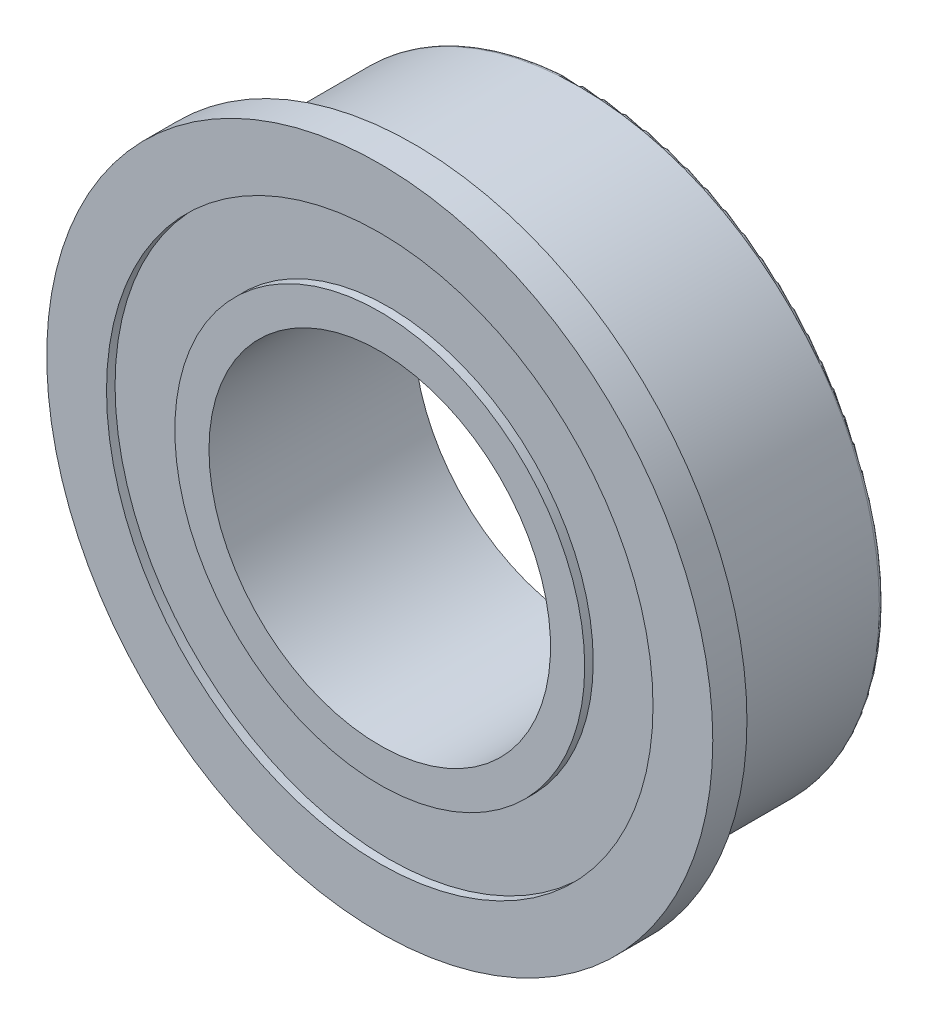
SolidWorks part; units mm, degrees
ref_plane "前基準面" through (0, 0, 0) normal (0, 0, 1) x (1, 0, 0)
ref_plane "上基準面" through (0, 0, 0) normal (0, 1, 0) x (1, 0, 0)
ref_plane "右基準面" through (0, 0, 0) normal (1, 0, 0) x (0, 0, -1)
sketch "草圖1" plane through (0, 0, 0) normal (0, 0, 1) x (1, 0, 0)
  circle A0 centre (0, 0) radius 7
  dimension "D1" = 14
extrude "填料-伸長1" add sketch "草圖1" along normal blind 4.8
sketch "草圖2" plane through (0, 0, 4.8) normal (0, 0, 1) x (1, 0, 0)
  circle A0 centre (0, 0) radius 7.8
  dimension "D1" = 15.6
extrude "填料-伸長2" add sketch "草圖2" against normal blind 0.8
sketch "草圖3" plane through (0, 0, 0) normal (0, 0, -1) x (-1, 0, 0)
  circle A0 centre (0, 0) radius 4
  dimension "D1" = 8
extrude "除料-伸長1" cut sketch "草圖3" against normal through all
sketch "草圖4" plane through (0, 0, 0) normal (0, 0, -1) x (-1, 0, 0)
  circle A0 centre (0, 0) radius 6.2
  circle A1 centre (0, 0) radius 4.8
  circle A2 centre (0, 0) radius 7 construction
  circle A3 centre (0, 0) radius 4 construction
  dimension "D1" = 0.8
  dimension "D2" = 0.8
extrude "除料-伸長2" cut sketch "草圖4" against normal blind 0.2
sketch "草圖5" plane through (0, 0, 4.8) normal (0, 0, 1) x (1, 0, 0)
  circle A0 centre (0, 0) radius 4.8
  circle A1 centre (0, 0) radius 6.4
  circle A2 centre (0, 0) radius 4 construction
  dimension "D1" = 0.8
  dimension "D2" = 1.6
extrude "除料-伸長3" cut sketch "草圖5" against normal blind 0.2
fillet "圓角1" radius 0.1 1 edges at (7, 0, 0)
